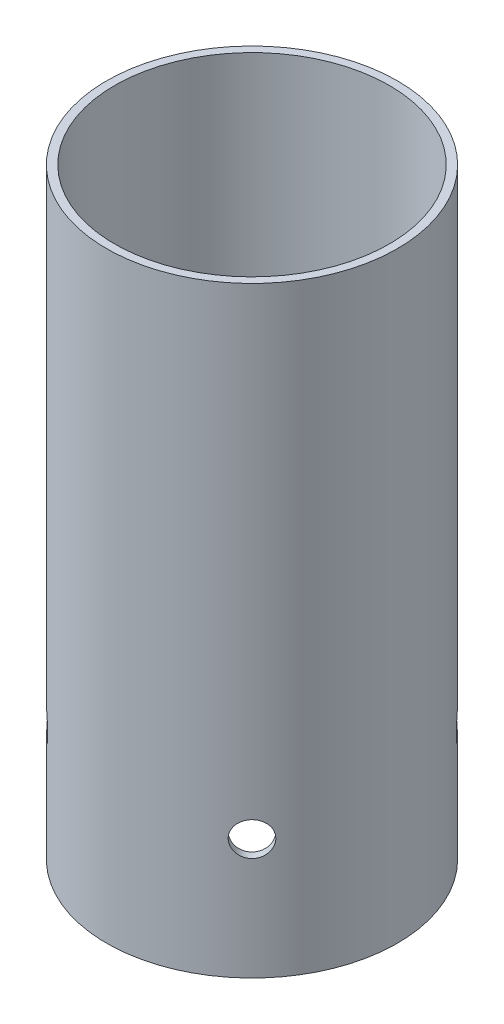
SolidWorks part; units mm, degrees
other "Top Tube"
ref_plane "Front Plane" through (0, 0, 0) normal (0, 0, 1) x (1, 0, 0)
ref_plane "Top Plane" through (0, 0, 0) normal (0, 1, 0) x (1, 0, 0)
ref_plane "Right Plane" through (0, 0, 0) normal (1, 0, 0) x (0, 0, -1)
sketch "Sketch1" plane through (0, 0, 0) normal (0, 0, 1) x (1, 0, 0)
  line L0 (55, 0) -> (-55, 0) construction
  line L1 (-15.35, 254) -> (-14.5, 254)
  line L2 (-15.35, 254) -> (-15.35, 317.5)
  line L3 (-15.35, 317.5) -> (-14.5, 317.5)
  line L4 (-14.5, 254) -> (-14.5, 317.5)
  line L5 (0, -55) -> (0, 55) construction
  line L6 (15.35, 317.5) -> (14.5, 317.5)
  line L7 (15.35, 254) -> (15.35, 317.5)
  line L8 (15.35, 254) -> (14.5, 254)
  line L9 (14.5, 254) -> (14.5, 317.5)
  line L10 (0, 0) -> (0, 330.2)
  dimension "D1" = 63.5
  dimension "9" = 254
  dimension "D2" = 30.7
  dimension "D3" = 29
revolve "Revolve1" add sketch "Sketch1" angle 360 about L10
ref_plane "Plane1" through (-10.8541, 0, 10.8541) normal (-0.7071, 0, 0.7071) x (0, -1, 0)
sketch "Sketch2" plane through (-10.8541, 0, 10.8541) normal (-0.7071, 0, 0.7071) x (0, -1, 0)
  line L0 (-254, -15.35) -> (-254, 15.35) construction
  circle A0 centre (-266.7, 0) radius 1.778
  dimension "D1" = 3.556
  dimension "D2" = 12.7
extrude "Cut-Extrude1" cut sketch "Sketch2" against normal blind 2.54
pattern_circular "CirPattern1" count 4 over 360 about axis through (0, 317.5, 0) along (0, -1, 0) of "Cut-Extrude1"
